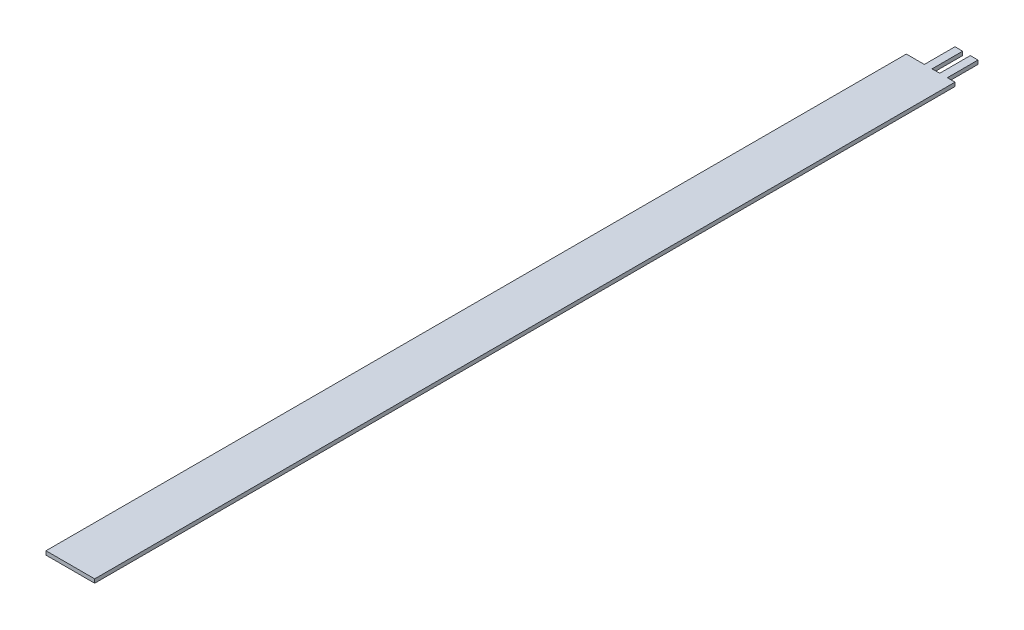
SolidWorks part; units mm, degrees
ref_plane "Front Plane" through (0, 0, 0) normal (0, 0, 1) x (1, 0, 0)
ref_plane "Top Plane" through (0, 0, 0) normal (0, 1, 0) x (1, 0, 0)
ref_plane "Right Plane" through (0, 0, 0) normal (1, 0, 0) x (0, 0, -1)
sketch "Sketch1" plane through (0, 0, 0) normal (0, 1, 0) x (1, 0, 0)
  line L0 (0, 0) -> (0, -112.24)
  line L1 (0, -112.24) -> (6.35, -112.24)
  line L2 (6.35, -112.24) -> (6.35, 0)
  line L3 (6.35, 0) -> (0, 0)
extrude "Boss-Extrude1" add sketch "Sketch1" along normal blind 0.5
sketch "Sketch2" plane through (0, 0, 0) normal (0, 0, -1) x (-1, 0, 0)
  line L0 (-6.35, 0.25) -> (0, 0.25) construction
  line L1 (-6.35, 0.5) -> (-6.35, 0) construction
  line L2 (0, 0.5) -> (0, 0) construction
  line L3 (-6.35, 0.25) -> (-5.35, 0.25) construction
  line L4 (-6.35, 0.5) -> (0, 0.5) construction
  line L5 (-5.35, 0.5) -> (-4.35, 0.5)
  line L6 (-5.35, 0.5) -> (-5.35, 0)
  line L7 (-5.35, 0) -> (-4.35, 0)
  line L8 (-4.35, 0.5) -> (-4.35, 0)
  line L9 (-6.35, 0) -> (0, 0) construction
  line L10 (-4.35, 0.25) -> (-3.35, 0.25)
  line L12 (-3.35, 0.5) -> (-2.35, 0.5)
  line L13 (-3.35, 0.5) -> (-3.35, 0)
  line L14 (-3.35, 0) -> (-2.35, 0)
  line L15 (-2.35, 0.5) -> (-2.35, 0)
  line M11 (-6.35, 0) -> (0, 0)
  line M13 (0, 0.5) -> (-6.35, 0.5)
extrude "Boss-Extrude2" add sketch "Sketch2" along normal blind 4 contours L15 L13 M13 M11 | L8 L6 M13 M11
